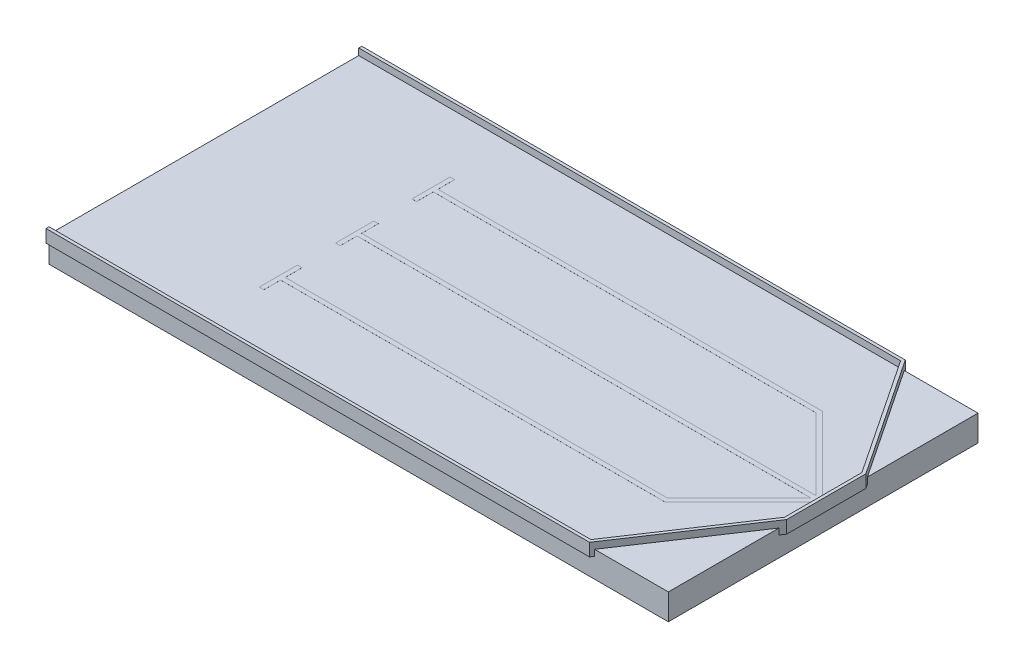
SolidWorks part; units mm, degrees
ref_plane "Front Plane" through (0, 0, 0) normal (0, 0, 1) x (1, 0, 0)
ref_plane "Top Plane" through (0, 0, 0) normal (0, 1, 0) x (1, 0, 0)
ref_plane "Right Plane" through (0, 0, 0) normal (1, 0, 0) x (0, 0, -1)
sketch "Sketch1" plane through (0, 0, 0) normal (0, 1, 0) x (1, 0, 0)
  line L1 (0, 0) -> (2438.4, 0)
  line L2 (0, 0) -> (0, 1219.2)
  line L3 (0, 1219.2) -> (2438.4, 1219.2)
  line L4 (2438.4, 0) -> (2438.4, 1219.2)
  dimension "D1" = 1219.2
  dimension "D2" = 2438.4
extrude "Boss-Extrude1" add sketch "Sketch1" along normal blind 102
sketch "Sketch2" plane through (0, 102, 0) normal (0, 1, 0) x (1, 0, 0)
  line L0 (0, 0) -> (2133.6, 0)
  line L1 (0, 0) -> (2438.4, 0) construction
  line L2 (2133.6, 0) -> (2438.4, 457.2)
  line L3 (2438.4, 0) -> (2438.4, 1219.2) construction
  line L4 (2438.4, 457.2) -> (2438.4, 762)
  line L5 (2438.4, 762) -> (2133.6, 1219.2)
  line L6 (2438.4, 1219.2) -> (0, 1219.2) construction
  line L7 (2133.6, 1219.2) -> (0, 1219.2)
  line L8 (2438.4, 609.6) -> (2223.1456, 609.6) construction
  point P5 (2438.4, 609.6)
  point P18 (2438.4, 609.6)
  dimension "D1" = 304.8
  dimension "D2" = 304.8
extrude "Extrude-Thin1" add sketch "Sketch2" along normal blind 26 and the other way blind 24 thin
sketch "Sketch3" plane through (0, 102, 0) normal (0, 1, 0) x (1, 0, 0)
  line L0 (2400.4, 618.6) -> (611.9859, 618.6)
  line L1 (611.9859, 618.6) -> (611.9859, 684.6)
  line L2 (611.9859, 684.6) -> (593.9859, 684.6)
  line L3 (593.9859, 684.6) -> (593.9859, 534.6)
  line L4 (593.9859, 609.6) -> (2797.8461, 609.6) construction
  line L5 (2438.4, 457.2) -> (2438.4, 762) construction
  line L7 (2400.4, 618.6) -> (2117.8, 901.2)
  line L8 (2117.8, 901.2) -> (611.9859, 901.2)
  line L9 (611.9859, 901.2) -> (611.9859, 835.2)
  line L10 (611.9859, 835.2) -> (593.9859, 835.2)
  line L11 (593.9859, 835.2) -> (593.9859, 985.2)
  line L12 (593.9859, 985.2) -> (611.9859, 985.2)
  line L13 (611.9859, 985.2) -> (611.9859, 919.2)
  line L14 (611.9859, 919.2) -> (2125.2558, 919.2)
  line L15 (2125.2558, 919.2) -> (2418.4, 626.0558)
  line L16 (2418.4, 626.0558) -> (2418.4, 593.1442)
  line L17 (2133.6, 1219.2) -> (0, 1219.2) construction
  line L18 (2125.2558, 300) -> (2418.4, 593.1442)
  line L19 (611.9859, 300) -> (2125.2558, 300)
  line L20 (611.9859, 234) -> (611.9859, 300)
  line L21 (593.9859, 234) -> (611.9859, 234)
  line L22 (593.9859, 384) -> (593.9859, 234)
  line L23 (611.9859, 384) -> (593.9859, 384)
  line L24 (611.9859, 318) -> (611.9859, 384)
  line L25 (2117.8, 318) -> (611.9859, 318)
  line L26 (2400.4, 600.6) -> (2117.8, 318)
  line L27 (611.9859, 534.6) -> (593.9859, 534.6)
  line L28 (611.9859, 600.6) -> (611.9859, 534.6)
  line L29 (2400.4, 600.6) -> (611.9859, 600.6)
  line L30 (0, 1219.2) -> (0, 0) construction
  point P8 (2438.4, 609.6)
  point P24 (2418.4, 609.6)
  dimension "D1" = 9
  dimension "D2" = 18
  dimension "D3" = 593.9859
  dimension "D4" = 75
  dimension "D5" = 150
  dimension "D6" = 18
  dimension "D7" = 66
  dimension "D8" = 18
  dimension "D9" = 300
  dimension "D10" = 45
  dimension "D11" = 18
  dimension "D12" = 18
  dimension "D13" = 20
extrude "Boss-Extrude2" add sketch "Sketch3" along normal blind 0.17
